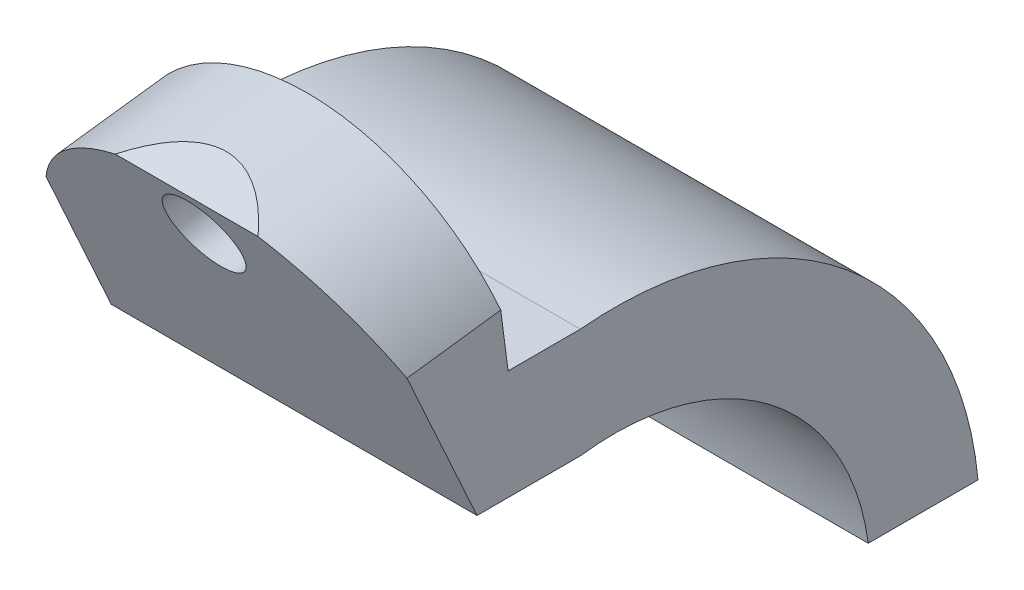
SolidWorks part; units mm, degrees
ref_plane "Front Plane" through (0, 0, 0) normal (0, 0, 1) x (1, 0, 0)
ref_plane "Top Plane" through (0, 0, 0) normal (0, 1, 0) x (1, 0, 0)
ref_plane "Right Plane" through (0, 0, 0) normal (1, 0, 0) x (0, 0, -1)
sketch "Sketch1" plane through (0, 0, 0) normal (1, 0, 0) x (0, 0, -1)
  line L0 (0, -20.4716) -> (30, -20.4716)
  line L1 (-78.7019, 39.5784) -> (-78.7019, 69.5784)
  arc A0 (0, -20.4716) -> (-78.7019, 39.5784) centre (-69.376, -29.7976) ccw
  arc A1 (30, -20.4716) -> (-78.7019, 69.5784) centre (-69.376, -29.7976) ccw
  dimension "D1" = 70
  dimension "D2" = 30
  dimension "D3" = 30
extrude "Boss-Extrude1" add sketch "Sketch1" along normal blind 100
sketch3d "3DSketch6"
  line L0 (100, 39.5784, 78.7019) -> (100, 39.5784, 94.8854)
  line L5 (100, 69.5784, 78.7019) -> (100, 69.5784, 98.4603)
  line L7 (100, 39.5784, 94.8854) -> (100, 39.5784, 106.9454)
  line L8 (100, 39.5784, 106.9454) -> (100, 51.9106, 112.5588)
  line L11 (100, 69.5784, 78.7019) -> (100, 39.5784, 78.7019)
  line L12 (100, 51.9106, 112.5588) -> (100, 105.8677, 137.1189)
  line L13 (100, 105.8677, 137.1189) -> (100, 120.4477, 105.0876)
  line L14 (100, 120.4477, 105.0876) -> (100, 69.5784, 98.4603)
extrude "Boss-Extrude15" add sketch "3DSketch6" along direction (1, 0, 0) on the side of the normal blind 100
sketch "Sketch12" plane through (0, -11.4523, 87.9034) normal (0, 0.1292, -0.9916) x (-1, 0, 0)
  circle A0 centre (-50, 109.8304) radius 10.5383
extrude "Cut-Extrude1" cut sketch "Sketch12" against normal blind 100
sketch "Sketch13" plane through (0, -11.4523, 87.9034) normal (0, 0.1292, -0.9916) x (-1, 0, 0)
  line L0 (-100, 133.0147) -> (-100, 81.7155) construction
  line L1 (0, 133.0147) -> (0, 81.7155) construction
  line L2 (-100, 97.257) -> (-100, 133.0147)
  line L4 (0, 133.0147) -> (0, 94.2088)
  line L5 (-100, 133.0147) -> (-100, 156.8309)
  line L6 (-100, 156.8309) -> (0, 160.198)
  line L7 (0, 160.198) -> (0, 133.0147)
  arc A2 (-100, 97.257) -> (0, 94.2088) centre (-50.7882, 69.8726) cw
extrude "Cut-Extrude4" cut sketch "Sketch13" against normal blind 100
